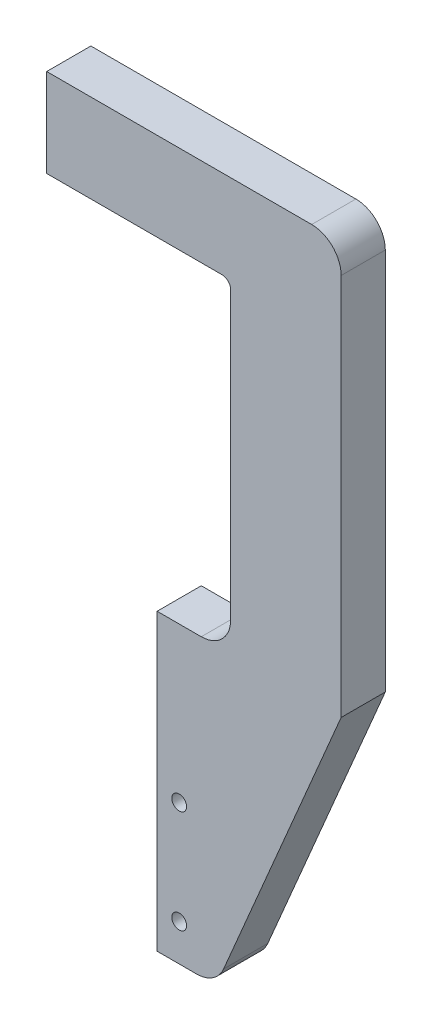
SolidWorks part; units mm, degrees
material "A3钢"
ref_plane "前视基准面" through (0, 0, 0) normal (0, 0, 1) x (1, 0, 0)
ref_plane "上视基准面" through (0, 0, 0) normal (0, 1, 0) x (1, 0, 0)
ref_plane "右视基准面" through (0, 0, 0) normal (1, 0, 0) x (0, 0, -1)
sketch "草图1" plane through (0, 0, 0) normal (0, 0, 1) x (1, 0, 0)
  line L0 (0, 0) -> (0, 30)
  line L1 (0, 30) -> (90, 30)
  line L2 (62.5, -110) -> (37.5, -110)
  line L3 (100, 20) -> (100, -110)
  line L4 (57.5, -210) -> (37.5, -210)
  line L5 (37.5, -110) -> (37.5, -210)
  line L7 (62.5, -110) -> (62.5, 0)
  line L8 (0, 0) -> (62.5, 0)
  line L9 (100, -110) -> (57.5, -210)
  arc A0 (100, 20) -> (90, 30) centre (90, 20) ccw
  dimension "D8" = 10
  dimension "D1" = 240
  dimension "D2" = 25
  dimension "D3" = 100
  dimension "D4" = 20
  dimension "D5" = 100
  dimension "D6" = 30
  dimension "D7" = 62.5
  dimension "D9" = 100
extrude "凸台-拉伸1" add sketch "草图1" along normal mid plane 15
hole_wizard "M8 螺纹孔1" positions "草图2" profile "草图3" tap size "M8" standard "GB"
sketch "草图2" plane through (0, 0, 0) normal (0, -1, 0) x (-1, 0, 0)
  line L0 (3.5744, 0) -> (-52.3707, 0) construction
  line L4 (0, -7.5) -> (0, 7.5) construction
  point P0 (-40, 0)
  point P2 (-10, 0)
  dimension "D1" = 10
  dimension "D2" = 30
sketch "草图3" plane through (40, 0, 0) normal (1, 0, 0) x (0, 0, -1)
  line L0 (0, 0) -> (0, 21.7929)
  line L1 (0, 21.7929) -> (3.4, 19.75)
  line L2 (3.4, 19.75) -> (3.4, 0)
  line L5 (3.4, 0) -> (0, 0)
  line L10 (0, 21.7929) -> (-3.4, 19.75) construction
  line L11 (0, -6.35) -> (0, 107.95) construction
  dimension "螺纹孔钻头直径" = 6.8
  dimension "螺纹孔钻头深度" = 19.75
  dimension "导头角度" = 118
cosmetic thread "孔螺蚊线1" parameters "D1"=16, "D2"=8
cosmetic thread "孔螺蚊线2" parameters "D1"=16, "D2"=8
hole_wizard "M8 螺纹孔2" positions "草图4" profile "草图5" tap size "M8" standard "GB"
sketch "草图4" plane through (37.5, 0, 0) normal (-1, 0, 0) x (0, 0, 1)
  line L0 (0, 12.873) -> (0, -174.2181) construction
  line L4 (7.5, -210) -> (-7.5, -210) construction
  point P0 (0, -130)
  point P2 (0, -190)
  dimension "D1" = 20
  dimension "D2" = 60
sketch "草图5" plane through (37.5, -130, 0) normal (0, 1, 0) x (0, 0, 1)
  line L0 (0, 0) -> (0, 21.7929)
  line L1 (0, 21.7929) -> (3.4, 19.75)
  line L2 (3.4, 19.75) -> (3.4, 0)
  line L5 (3.4, 0) -> (0, 0)
  line L10 (0, 21.7929) -> (-3.4, 19.75) construction
  line L11 (0, -6.35) -> (0, 107.95) construction
  dimension "螺纹孔钻头直径" = 6.8
  dimension "螺纹孔钻头深度" = 19.75
  dimension "导头角度" = 118
cosmetic thread "孔螺蚊线3" parameters "D1"=16, "D2"=8
cosmetic thread "孔螺蚊线4" parameters "D1"=16, "D2"=8
fillet "圆角1" radius 10 2 edges at (62.5, -110, 0) (57.5, -210, 0)
fillet "圆角2" radius 3 1 edges at (62.5, 0, 0)
sketch "草图6" plane through (0, 0, 7.5) normal (0, 0, 1) x (1, 0, 0)
  line L0 (45, -197.5) -> (45, -162.5) construction
  line L1 (37.5, -110) -> (37.5, -210) construction
  line L2 (37.5, -210) -> (50.8843, -210) construction
  dimension "D1" = 7.5
  dimension "D2" = 35
  dimension "D3" = 12.5
hole_wizard "M6 螺纹孔1" positions "3D草图1" profile "草图7" tap size "M6" standard "GB" end condition through all
sketch3d "3D草图1"
  point P0 (45, -162.5, 7.5)
  point P3 (45, -197.5, 7.5)
cosmetic thread "孔螺蚊线5" parameters "D2"=6
cosmetic thread "孔螺蚊线6" parameters "D2"=6
sketch "草图7" plane through (45, -162.5, 7.5) normal (1, 0, 0) x (0, -1, 0)
  line L0 (0, 0) -> (0, 15)
  line L1 (0, 15) -> (2.5, 15)
  line L2 (2.5, 15) -> (2.5, 0)
  line L5 (2.5, 0) -> (0, 0)
  line L11 (0, -6.35) -> (0, 107.95) construction
  dimension "通孔螺纹孔钻头直径" = 5
  dimension "通孔螺纹孔钻头深度" = 15
